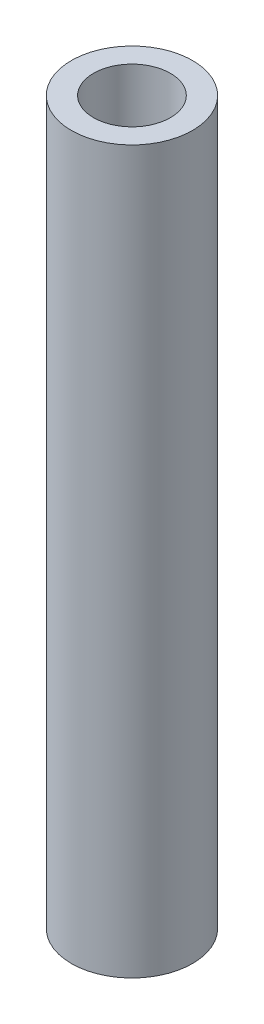
SolidWorks part; units mm, degrees
ref_plane "Front Plane" through (0, 0, 0) normal (0, 0, 1) x (1, 0, 0)
ref_plane "Top Plane" through (0, 0, 0) normal (0, 1, 0) x (1, 0, 0)
ref_plane "Right Plane" through (0, 0, 0) normal (1, 0, 0) x (0, 0, -1)
sketch "Sketch3" plane through (0, 0, 0) normal (0, 1, 0) x (1, 0, 0)
  line L0 (-88.0337, 0) -> (88.0337, 0) construction
  line L1 (0, 60.6068) -> (0, -60.6068) construction
  circle A0 centre (0, 0) radius 4.1
  circle A1 centre (0, 0) radius 2.6023
  point P4 (0, 0)
  point P8 (0, 0)
  dimension "D1" = 5.2045
  dimension "D2" = 8.2
extrude "Boss-Extrude3" add sketch "Sketch3" along normal mid plane 48.81
